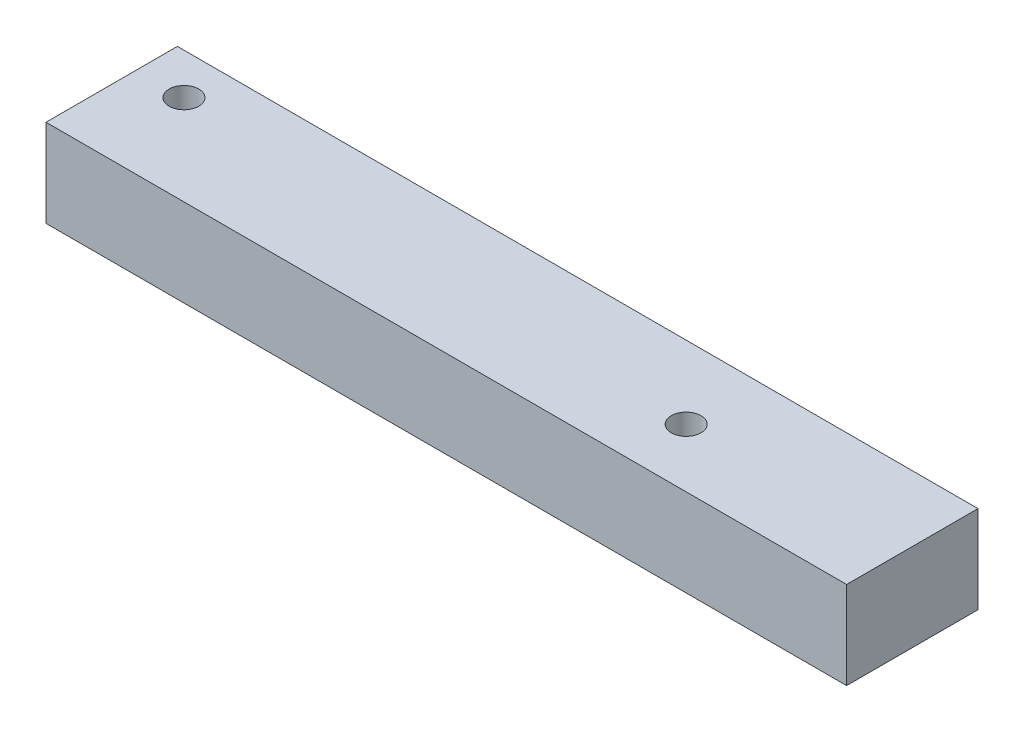
SolidWorks part; units mm, degrees
ref_plane "Front Plane" through (0, 0, 0) normal (0, 0, 1) x (1, 0, 0)
ref_plane "Top Plane" through (0, 0, 0) normal (0, 1, 0) x (1, 0, 0)
ref_plane "Right Plane" through (0, 0, 0) normal (1, 0, 0) x (0, 0, -1)
sketch "Sketch2" plane through (0, 0, 0) normal (0, 1, 0) x (1, 0, 0)
  line L0 (-44.1621, 83.2812) -> (47.2342, 83.2812)
  line L1 (14.2342, 68.2813) -> (47.2342, 68.2813)
  line L2 (47.2342, 68.2813) -> (47.2342, 83.2812)
  line L3 (14.2342, 68.2813) -> (-44.1621, 68.2813)
  line L5 (-44.1621, 68.2813) -> (-44.1621, 83.2812)
  circle A0 centre (-38.7191, 78.588) radius 1.7
  circle A1 centre (22.2342, 74.9633) radius 1.7
extrude "Boss-Extrude2" add sketch "Sketch2" along normal blind 10
